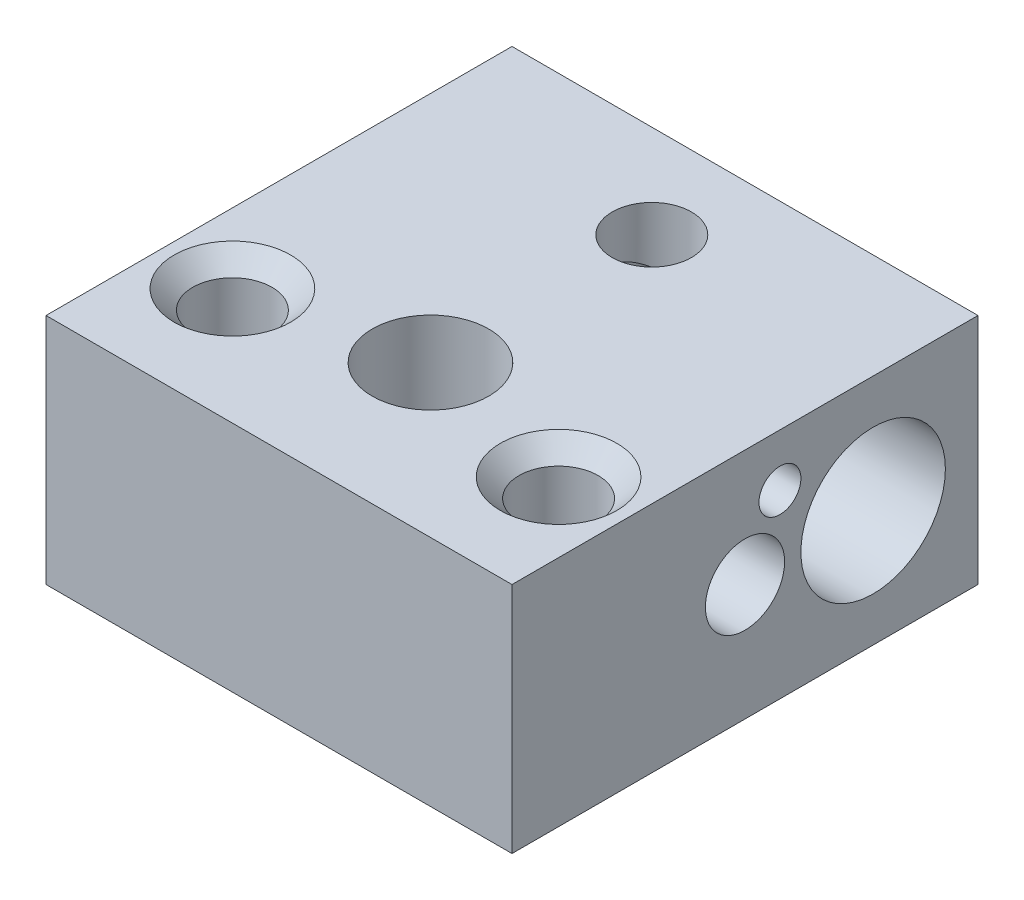
SolidWorks part; units mm, degrees
material "Aleación 1060"
ref_plane "Alzado" through (0, 0, 0) normal (0, 0, 1) x (1, 0, 0)
ref_plane "Planta" through (0, 0, 0) normal (0, 1, 0) x (1, 0, 0)
ref_plane "Vista lateral" through (0, 0, 0) normal (1, 0, 0) x (0, 0, -1)
sketch "Croquis1" plane through (0, 0, 0) normal (0, 1, 0) x (1, 0, 0)
  line L1 (-10, -10) -> (10, -10)
  line L2 (-10, -10) -> (-10, 10)
  line L3 (-10, 10) -> (10, 10)
  line L4 (10, -10) -> (10, 10)
  line L5 (-10, -10) -> (10, 10) construction
  line L6 (-10, 10) -> (10, -10) construction
  point P0 (0, 0)
  dimension "D1" = 20
  dimension "D2" = 20
extrude "Saliente-Extruir1" add sketch "Croquis1" along normal blind 10
hole_wizard "Perforador para roscar para macho de roscar para M6x1.01" positions "Croquis4" profile "Croquis5" hole size "M6x1.0" standard "Ansi Metric" end condition through all
sketch "Croquis4" plane through (0, 10, 0) normal (0, 1, 0) x (1, 0, 0)
  line L0 (-10, -10) -> (10, -10) construction
  line L1 (-10, 10) -> (-10, -10) construction
  point P0 (0, -3.5)
  dimension "D1" = 6.5
  dimension "D2" = 10
sketch "Croquis5" plane through (0, 10, 3.5) normal (1, 0, 0) x (0, 0, 1)
  line L0 (0, 0) -> (0, 10)
  line L1 (0, 10) -> (2.5, 10)
  line L2 (2.5, 10) -> (2.5, 0)
  line L5 (2.5, 0) -> (0, 0)
  line L11 (0, -6.35) -> (0, 107.95) construction
  dimension "Diámetro de taladro hasta el siguiente" = 5
  dimension "Profundidad de taladro hasta el siguiente" = 10
thread "Rosca1" pitch 1 start angle 0, offset 0, length 0, pitch 1, diameter 5
ref_plane "Plano1" through (-2.5, 10, 3.5) normal (0, 0, 1) x (-1, 0, 0)
sketch "Perfil de rosca1" plane through (-2.5, 10, 3.5) normal (0, 0, 1) x (-1, 0, 0)
  line L0 (0, 0) -> (0, 1) construction
  line L11 (0, 0) -> (0, 0.875)
  line L12 (0, 0.875) -> (-0.5413, 0.5625)
  line L13 (-0.5413, 0.5625) -> (-0.5413, 0.3125)
  line L15 (-0.5413, 0.3125) -> (0, 0)
  line L17 (-0.5413, 0.4375) -> (0, 0.4375) construction
  point P2 (0, 0)
  dimension "Pitch" = 1
  dimension "Profile_Angle" = 60
  dimension "Profile_Land" = 0.25
  dimension "Profile_Height" = 0.5413
hole_wizard "Refrentado para tornillo tapón con cabeza plana de clavija de M31" positions "Croquis8" profile "Croquis9" countersink size "M3" standard "Ansi Metric" end condition through all
sketch "Croquis8" plane through (0, 10, 0) normal (0, 1, 0) x (1, 0, 0)
  line L0 (-10, -10) -> (10, -10) construction
  line L2 (-10, 10) -> (-10, -10) construction
  line L3 (10, -10) -> (10, 10) construction
  point P0 (-7, -5)
  point P2 (7, -5)
  dimension "D1" = 5
  dimension "D2" = 5
  dimension "D3" = 3
  dimension "D4" = 3
sketch "Croquis9" plane through (-7, 10, 5) normal (1, 0, 0) x (0, 0, 1)
  line L0 (0, 0) -> (0, 10)
  line L1 (0, 10) -> (1.7, 10)
  line L2 (1.7, 10) -> (1.7, 0.8)
  line L3 (1.7, 0.8) -> (2.5, 0)
  line L5 (2.5, 0) -> (0, 0)
  line L6 (-1.7, 0.8) -> (-2.5, 0) construction
  line L11 (0, -6.35) -> (0, 107.95) construction
  dimension "Diámetro de taladro hasta el siguiente" = 3.4
  dimension "Profundidad de taladro hasta el siguiente" = 10
  dimension "Diámetro de avellanado cercano" = 5
  dimension "Ángulo de avellanado cercano" = 90
hole_wizard "Taladro de margen para M31" positions "Croquis14" profile "Croquis16" hole size "M3" standard "Ansi Metric" end condition through all
sketch "Croquis14" plane through (0, 10, 0) normal (0, 1, 0) x (1, 0, 0)
  line L0 (10, 10) -> (-10, 10) construction
  line L1 (10, -10) -> (10, 10) construction
  point P0 (0, 6)
  dimension "D1" = 4
  dimension "D2" = 10
sketch "Croquis16" plane through (0, 10, -6) normal (1, 0, 0) x (0, 0, 1)
  line L0 (0, 0) -> (0, 10)
  line L1 (0, 10) -> (1.7, 10)
  line L2 (1.7, 10) -> (1.7, 0)
  line L5 (1.7, 0) -> (0, 0)
  line L11 (0, -6.35) -> (0, 107.95) construction
  dimension "Diámetro de taladro hasta el siguiente" = 3.4
  dimension "Profundidad de taladro hasta el siguiente" = 10
sketch "Croquis17" plane through (10, 0, 0) normal (1, 0, 0) x (0, 0, -1)
  line L0 (-10, 10) -> (-10, 0) construction
  line L1 (-10, 0) -> (10, 0) construction
  circle A0 centre (5.5, 5) radius 3.1
  dimension "D1" = 6.2
  dimension "D2" = 15.5
  dimension "D3" = 5
extrude "Cortar-Extruir1" cut sketch "Croquis17" against normal blind 20
hole_wizard "Taladro de margen para M32" positions "Croquis18" profile "Croquis20" hole size "M3" standard "Ansi Metric"
sketch "Croquis18" plane through (10, 0, 0) normal (-1, 0, 0) x (0, 0, 1)
  line L0 (10, 10) -> (10, 0) construction
  line L1 (-10, 10) -> (10, 10) construction
  point P0 (0, 5)
  dimension "D1" = 10
  dimension "D2" = 5
sketch "Croquis20" plane through (10, 5, 0) normal (0, 1, 0) x (0, 0, -1)
  line L0 (0, 0) -> (0, 7)
  line L1 (0, 7) -> (1.7, 7)
  line L2 (1.7, 7) -> (1.7, 0)
  line L5 (1.7, 0) -> (0, 0)
  line L10 (0, 7) -> (-1.7, 7) construction
  line L11 (0, -6.35) -> (0, 107.95) construction
  dimension "Diámetro de taladro" = 3.4
  dimension "Profundidad de taladro" = 7
  dimension "Ángulo de perforador" = 180
sketch "Croquis21" plane through (10, 0, 0) normal (-1, 0, 0) x (0, 0, 1)
  circle A1 centre (0, 5) radius 1.7 construction
  circle A3 centre (-1.5, 7.75) radius 0.9
  dimension "D4" = 1.8
  dimension "D5" = 2.75
  dimension "D6" = 1.5
extrude "Cortar-Extruir2" cut sketch "Croquis21" along normal blind 2.75
